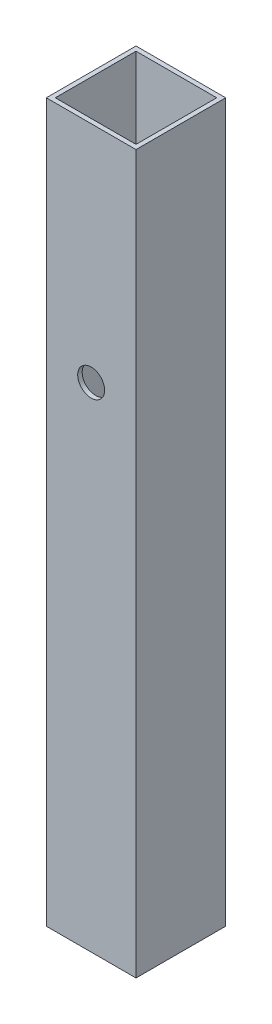
SolidWorks part; units mm, degrees
ref_plane "Front" through (0, 0, 0) normal (0, 0, 1) x (1, 0, 0)
ref_plane "Top" through (0, 0, 0) normal (0, 1, 0) x (1, 0, 0)
ref_plane "Right" through (0, 0, 0) normal (1, 0, 0) x (0, 0, -1)
sketch "草图1" plane through (0, 0, 0) normal (0, 1, 0) x (1, 0, 0)
  line L0 (-18.0928, 0) -> (21.4607, 0) construction
  line L1 (0, 24.5757) -> (0, -21.0047) construction
  line L3 (-10, 10) -> (10, 10)
  line L4 (-10, 10) -> (-10, -10)
  line L5 (-10, -10) -> (10, -10)
  line L6 (10, 10) -> (10, -10)
  line L7 (-9, 9) -> (9, 9)
  line L8 (-9, 9) -> (-9, -9)
  line L9 (-9, -9) -> (9, -9)
  line L10 (9, 9) -> (9, -9)
  dimension "D1" = 20
  dimension "D2" = 20
  dimension "D3" = 10
  dimension "D4" = 10
  dimension "D5" = 9
  dimension "D6" = 18
  dimension "D7" = 18
  dimension "D8" = 9
extrude "凸台-拉伸1" add sketch "草图1" along normal blind 140
sketch "草图2" plane through (0, 0, 0) normal (0, -1, 0) x (1, 0, 0)
  line L1 (-10, 10) -> (10, 10)
  line L2 (-10, 10) -> (-10, -10)
  line L3 (-10, -10) -> (10, -10)
  line L4 (10, 10) -> (10, -10)
extrude "凸台-拉伸2" add sketch "草图2" along normal blind 20
sketch "草图3" plane through (0, 0, 10) normal (0, 0, 1) x (1, 0, 0)
  line L0 (0, 140) -> (0, -20) construction
  line L1 (-10, 140) -> (10, 140) construction
  line L2 (10, -20) -> (-10, -20) construction
  circle A0 centre (0, 90) radius 3
  dimension "D1" = 50
extrude "切除-拉伸1" cut sketch "草图3" against normal blind 2
